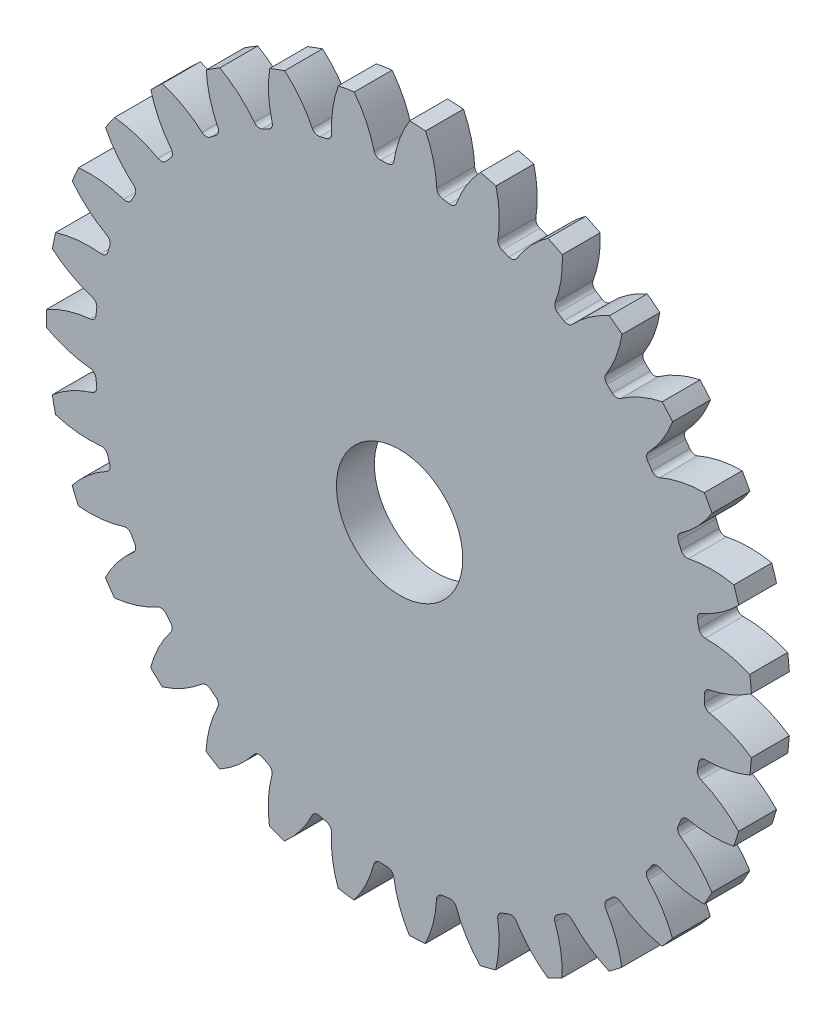
SolidWorks part; units mm, degrees
ref_plane "Alzado" through (0, 0, 0) normal (0, 0, 1) x (1, 0, 0)
ref_plane "Planta" through (0, 0, 0) normal (0, 1, 0) x (1, 0, 0)
ref_plane "Vista lateral" through (0, 0, 0) normal (1, 0, 0) x (0, 0, -1)
sketch "Croquis1" plane through (0, 0, 0) normal (0, 0, 1) x (1, 0, 0)
  circle A0 centre (0, 0) radius 27.94
  dimension "D1" = 55.88
extrude "Saliente-Extruir1" add sketch "Croquis1" along normal blind 3
sketch "Croquis2" plane through (0, 0, 3) normal (0, 0, 1) x (1, 0, 0)
  line L0 (0, 0) -> (0, 26.289) construction
  line L1 (0, 0) -> (9.8656, 27.1054) construction
  line L2 (0, 0) -> (-1.3208, 26.2558) construction
  line L3 (0, 26.289) -> (8.4491, 23.2138) construction
  arc A0 (0.7932, 27.9287) -> (-3.592, 27.7081) centre (0, 0) ccw
  arc A3 (-0.496, 24.1249) -> (-1.9276, 24.0529) centre (0, 0) ccw
  arc A4 (0.7932, 27.9287) -> (-0.496, 24.1249) centre (8.4491, 23.2138) ccw
  arc A5 (-3.592, 27.7081) -> (-1.9276, 24.0529) centre (-10.7361, 22.2487) cw
  dimension "D2" = 48.26
  dimension "D3" = 20
  dimension "D4" = 1.3208
extrude "Cortar-Extruir1" cut sketch "Croquis2" against normal through all
fillet "Redondeo1" radius 0.508 2 edges at (-0.496, 24.1249, 1.5) (-1.9276, 24.0529, 1.5)
pattern_circular "MatrizC1" count 31 over 360 about axis through (0, 0, 0) along (0, 0, 1) of "Redondeo1", "Cortar-Extruir1"
sketch "Croquis3" plane through (0, 0, 3) normal (0, 0, 1) x (1, 0, 0)
  circle A0 centre (0, 0) radius 5
  dimension "D1" = 10
extrude "Cortar-Extruir2" cut sketch "Croquis3" against normal through all
